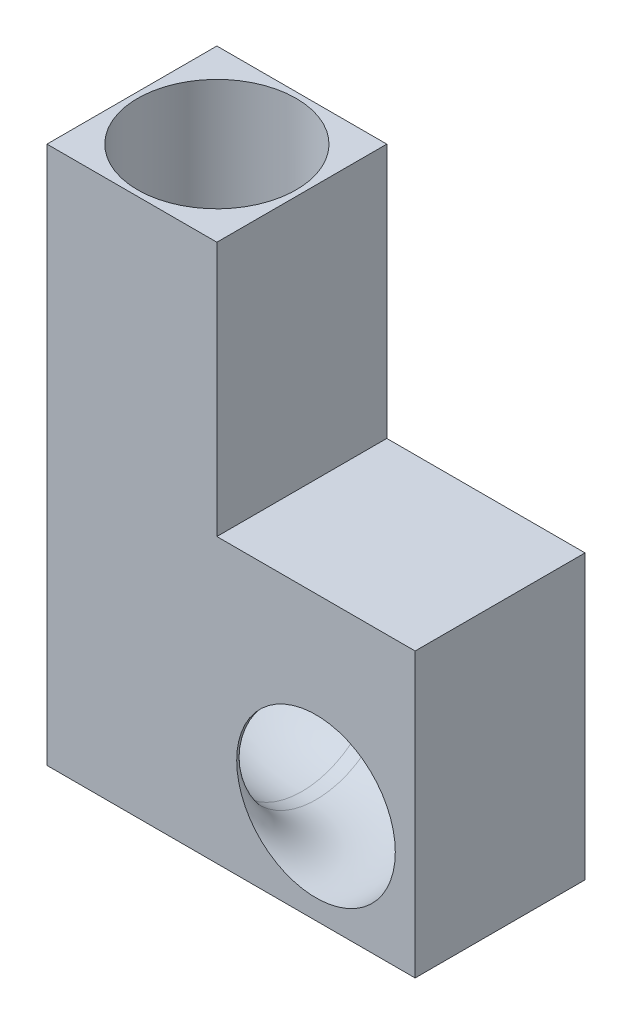
SolidWorks part; units mm, degrees
ref_plane "Front Plane" through (0, 0, 0) normal (0, 0, 1) x (1, 0, 0)
ref_plane "Top Plane" through (0, 0, 0) normal (0, 1, 0) x (1, 0, 0)
ref_plane "Right Plane" through (0, 0, 0) normal (1, 0, 0) x (0, 0, -1)
sketch "Sketch1" plane through (0, 0, 0) normal (0, 0, 1) x (1, 0, 0)
  line L0 (0, 241.3) -> (0, 0)
  line L1 (0, 0) -> (165.1, 0)
  line L2 (165.1, 0) -> (165.1, 127)
  line L3 (165.1, 127) -> (76.2, 127)
  line L4 (76.2, 127) -> (76.2, 241.3)
  line L5 (76.2, 241.3) -> (0, 241.3)
  dimension "D1" = 165.1
  dimension "D2" = 241.3
  dimension "D3" = 76.2
  dimension "D4" = 127
extrude "Boss-Extrude1" add sketch "Sketch1" along normal blind 76.2
sketch3d "3DSketch1"
  line L0 (38.1, 241.3, 38.1) -> (38.1, 82.55, 38.1)
  line L1 (76.2, 44.45, 38.1) -> (82.55, 44.45, 38.1)
  line L2 (76.2, 241.3, 76.2) -> (0, 241.3, 76.2) construction
  line L3 (76.2, 241.3, 76.2) -> (76.2, 241.3, 0) construction
  line L4 (0, 241.3, 76.2) -> (0, 0, 76.2) construction
  line L5 (0, 0, 76.2) -> (165.1, 0, 76.2) construction
  arc A0 (38.1, 82.55, 38.1) -> (76.2, 44.45, 38.1) centre (76.2, 82.55, 38.1) ccw
  arc A1 (120.65, 44.45, 76.2) -> (82.55, 44.45, 38.1) centre (82.55, 44.45, 76.2) ccw
  point P4 (76.2, 82.55, 76.2)
  point P18 (82.55, 82.55, 76.2)
  dimension "D4" = 38.1
  dimension "D6" = 38.1
  dimension "D1" = 38.1
  dimension "D2" = 38.1
  dimension "D3" = 120.65
  dimension "D5" = 44.45
sketch "Sketch2" plane through (0, 241.3, 0) normal (0, 1, 0) x (1, 0, 0)
  circle A0 centre (38.1, -38.1) radius 35.56
  dimension "D1" = 71.12
sweep "Cut-Sweep1" cut profiles "Sketch2" path "3DSketch1"
